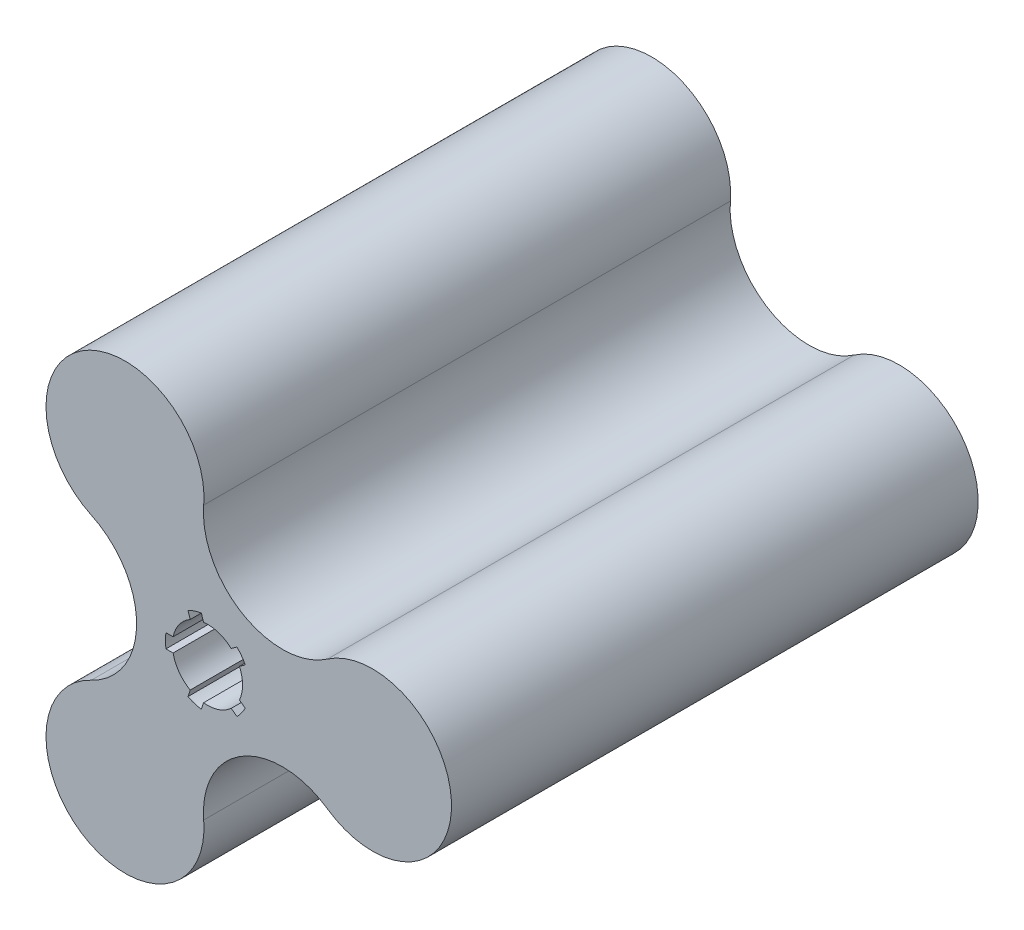
SolidWorks part; units mm, degrees
ref_plane "Ön Düzlem" through (0, 0, 0) normal (0, 0, 1) x (1, 0, 0)
ref_plane "Üst Düzlem" through (0, 0, 0) normal (0, 1, 0) x (1, 0, 0)
ref_plane "Sağ Düzlem" through (0, 0, 0) normal (1, 0, 0) x (0, 0, -1)
sketch "Çizim1" plane through (0, 0, 0) normal (0, 0, 1) x (1, 0, 0)
  line L0 (0, 0) -> (-12, 0) construction
  line L1 (-1.7542, 11.8711) -> (-1.1256, 9.9364)
  line L2 (-11.8322, 2) -> (-9.798, 2)
  line L3 (-11.8322, -2) -> (-9.798, -2)
  line L4 (-5.5585, 10.635) -> (-4.9298, 8.7004)
  line L5 (10.748, 5.3367) -> (9.1023, 4.1411)
  line L6 (8.3968, 8.5728) -> (6.7511, 7.3771)
  line L7 (8.3968, -8.5728) -> (6.7511, -7.3771)
  line L8 (10.748, -5.3367) -> (9.1023, -4.1411)
  line L9 (-5.5585, -10.635) -> (-4.9298, -8.7004)
  line L10 (-1.7542, -11.8711) -> (-1.1256, -9.9364)
  line L11 (0, 0) -> (47, 0) construction
  circle A0 centre (0, 0) radius 10
  arc A1 (-11.8322, 2) -> (-11.8322, -2) centre (0, 0) ccw
  arc A2 (-1.7542, 11.8711) -> (-5.5585, 10.635) centre (0, 0) ccw
  arc A3 (10.748, 5.3367) -> (8.3968, 8.5728) centre (0, 0) ccw
  arc A4 (8.3968, -8.5728) -> (10.748, -5.3367) centre (0, 0) ccw
  arc A5 (-5.5585, -10.635) -> (-1.7542, -11.8711) centre (0, 0) ccw
  arc A6 (34.1725, -18.4852) -> (34.1725, 18.4852) centre (47, 0) ccw
  arc A7 (-33.0949, -20.3516) -> (-1.0775, -38.8368) centre (-23.5, -40.7032) ccw
  arc A8 (-1.0775, 38.8368) -> (-33.0949, 20.3516) centre (-23.5, 40.7032) ccw
  arc A9 (-1.0775, -38.8368) -> (34.1725, -18.4852) centre (21.3449, -36.9705) cw
  arc A10 (-33.0949, -20.3516) -> (-33.0949, 20.3516) centre (-42.6898, 0) ccw
  arc A11 (34.1725, 18.4852) -> (-1.0775, 38.8368) centre (21.3449, 36.9705) cw
  point P8 (-12, 0)
  point P28 (0, 0)
  point P35 (0, 0)
  dimension "D1" = 20
  dimension "D2" = 24
  dimension "D7" = 45
  dimension "D10" = 23.5
  dimension "D12" = 22.5
  dimension "D13" = 22.5
  dimension "D8" = 40.7032
  dimension "D9" = 3
  dimension "D11" = 22.5
  dimension "D3" = 2
  dimension "D4" = 2
  dimension "D6" = 47
  dimension "D5" = 5
extrude "Yükseklik-Ekstrüzyon1" add sketch "Çizim1" against normal blind 150 contours A6 A11 A8 A10 A7 A9 A5 L9 A0 L3 A1 L2 L4 A2 L1 L6 A3 L5 L8 A4 L7 L10
